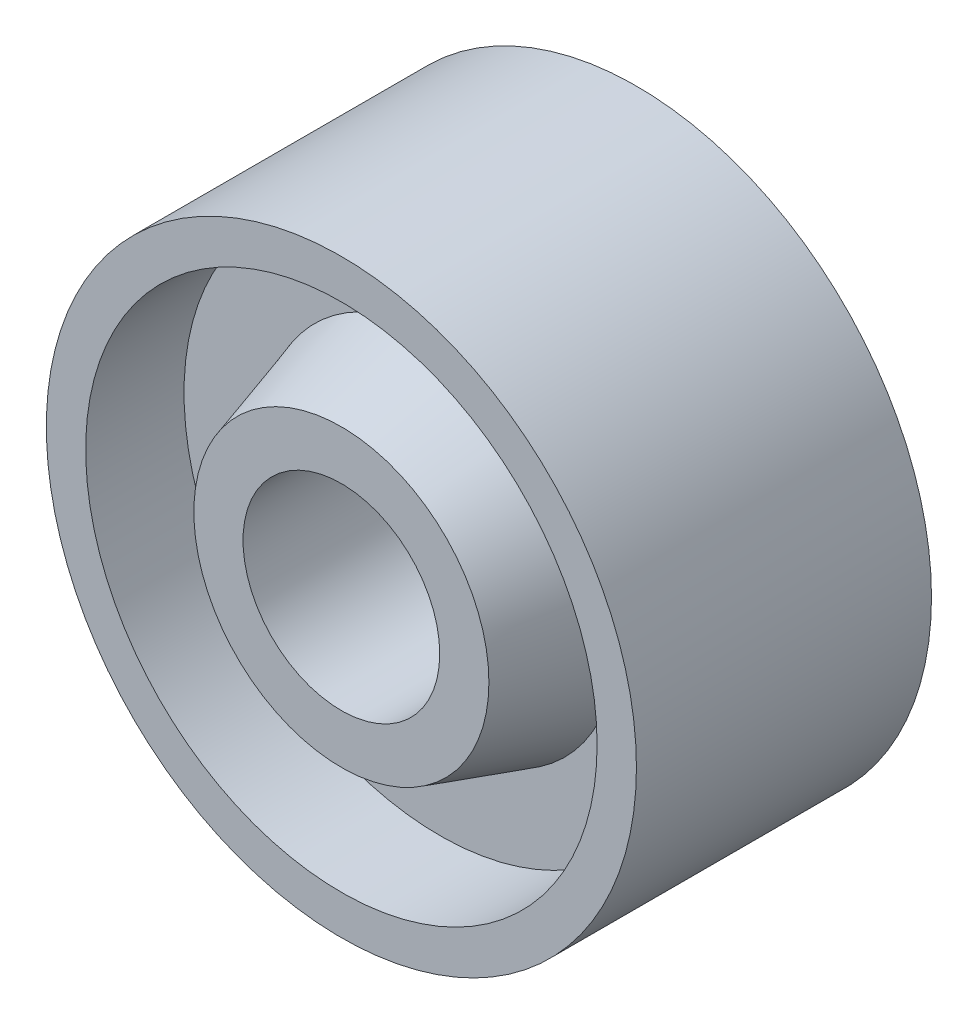
SolidWorks part; units mm, degrees
ref_plane "Ön Düzlem" through (0, 0, 0) normal (0, 0, 1) x (1, 0, 0)
ref_plane "Üst Düzlem" through (0, 0, 0) normal (0, 1, 0) x (1, 0, 0)
ref_plane "Sağ Düzlem" through (0, 0, 0) normal (1, 0, 0) x (0, 0, -1)
sketch "Çizim1" plane through (0, 0, 0) normal (0, 0, 1) x (1, 0, 0)
  line L0 (0, 46.0581) -> (0, -52.9884) construction
  circle A0 centre (0, 0) radius 30
  dimension "D1" = 60
extrude "Yükseklik-Ekstrüzyon1" add sketch "Çizim1" against normal blind 30
sketch "Çizim2" plane through (0, 0, 0) normal (0, 0, 1) x (1, 0, 0)
  circle A0 centre (0, 0) radius 26
  dimension "D1" = 52
extrude "Kes-Ekstrüzyon1" cut sketch "Çizim2" against normal blind 10
sketch "Çizim3" plane through (0, 0, -30) normal (0, 0, -1) x (-1, 0, 0)
  circle A0 centre (0, 0) radius 26
  dimension "D1" = 52
extrude "Kes-Ekstrüzyon2" cut sketch "Çizim3" against normal blind 10
sketch "Çizim4" plane through (0, 0, -10) normal (0, 0, 1) x (1, 0, 0)
  circle A0 centre (0, 0) radius 10
  circle A1 centre (0, 0) radius 15
  dimension "D1" = 30
  dimension "D2" = 20
extrude "Kes-Ekstrüzyon3" cut sketch "Çizim4" against normal blind 10 contours A0
sketch "Çizim6" plane through (0, 0, -10) normal (0, 0, 1) x (1, 0, 0)
  circle A0 centre (0, 0) radius 15
  circle A1 centre (0, 0) radius 10
  dimension "D1" = 30
  dimension "D2" = 20
extrude "Yükseklik-Ekstrüzyon3" add sketch "Çizim6" along normal blind 10 contours A0
sketch "Çizim7" plane through (0, 0, 0) normal (0, 0, 1) x (1, 0, 0)
  circle A0 centre (0, 0) radius 10
  dimension "D1" = 20
extrude "Kes-Ekstrüzyon4" cut sketch "Çizim7" against normal blind 10
sketch "Çizim8" plane through (0, 0, -20) normal (0, 0, -1) x (-1, 0, 0)
  circle A0 centre (0, 0) radius 15
  dimension "D1" = 30
extrude "Yükseklik-Ekstrüzyon4" add sketch "Çizim8" along normal blind 10
sketch "Çizim9" plane through (0, 0, -30) normal (0, 0, -1) x (-1, 0, 0)
  circle A0 centre (0, 0) radius 10
  dimension "D1" = 20
extrude "Kes-Ekstrüzyon5" cut sketch "Çizim9" against normal blind 10
ref_plane "Düzlem1" through (0, 0, -10) normal (0, 0, 1) x (1, 0, 0)
sketch "Çizim11" plane through (0, 0, -10) normal (0, 0, 1) x (1, 0, 0)
  line L0 (0, 15) -> (0, 18)
  circle A0 centre (0, 0) radius 15
  dimension "D1" = 30
  dimension "D2" = 3
sketch "Çizim12" plane through (0, 0, 0) normal (1, 0, 0) x (0, 0, -1)
  line L0 (10, 18) -> (0, 15)
  line L1 (10, 18) -> (10, 15)
  line L2 (10, 15) -> (0, 15)
  line L3 (0, 0) -> (27.6124, 0) construction
revolve "Döndür1" add sketch "Çizim12" angle 360 about L3
ref_plane "Düzlem2" through (0, 0, -15) normal (0, 0, 1) x (1, 0, 0)
mirror "Aynalama1" about plane through (0, 0, -15) normal (0, 0, 1) of "Döndür1"
